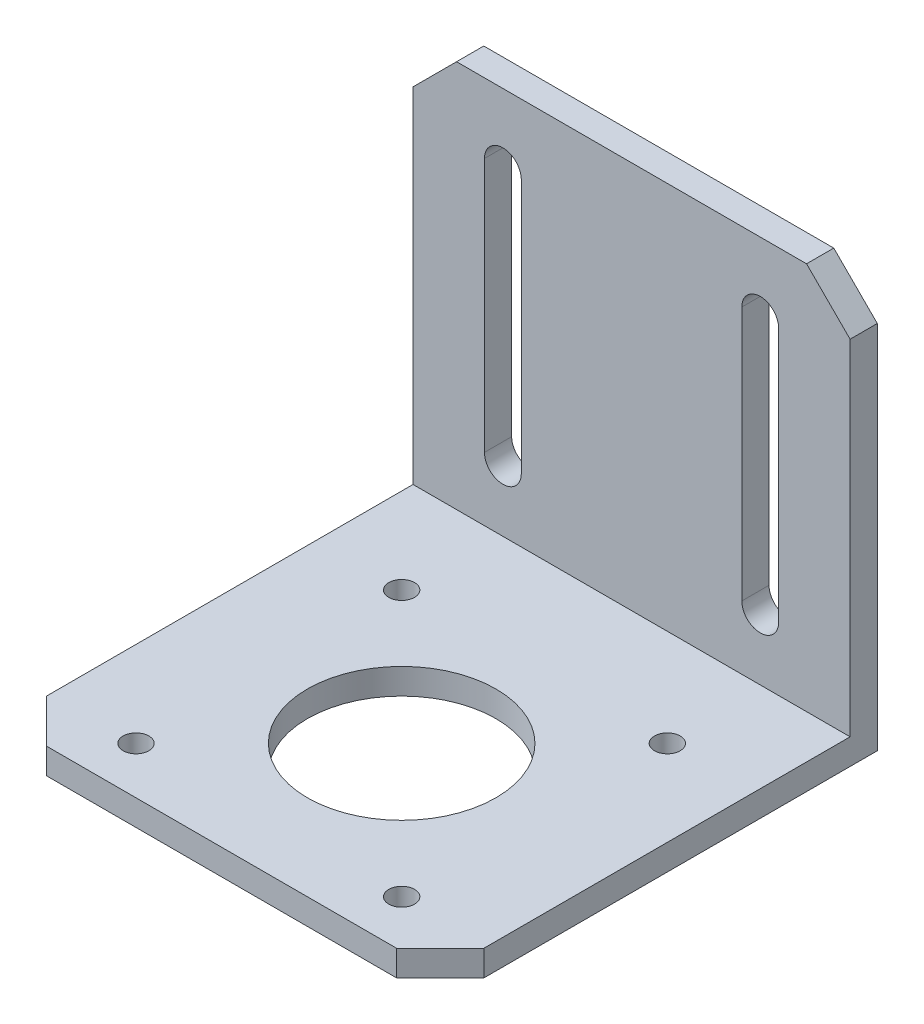
SolidWorks part; units mm, degrees
ref_plane "Front Plane" through (0, 0, 0) normal (0, 0, 1) x (1, 0, 0)
ref_plane "Top Plane" through (0, 0, 0) normal (0, 1, 0) x (1, 0, 0)
ref_plane "Right Plane" through (0, 0, 0) normal (1, 0, 0) x (0, 0, -1)
sketch "Sketch1" plane through (0, 0, 0) normal (0, 1, 0) x (1, 0, 0)
  line L0 (0, -1000) -> (0, 49000) construction
  line L5 (20.42, -21) -> (-20.42, -21)
  line L6 (25.5, -15.92) -> (25.5, 30)
  line L7 (25.5, 30) -> (-25.5, 30)
  line L8 (-25.5, -15.92) -> (-25.5, 30)
  line L9 (-1000, 0) -> (49000, 0) construction
  line L10 (25.5, -15.92) -> (20.42, -21)
  line L11 (-20.42, -21) -> (-25.5, -15.92)
  circle A5 centre (0, 0) radius 11
  circle A6 centre (15.5, -15.5) radius 1.5
  circle A7 centre (-15.5, -15.5) radius 1.5
  circle A8 centre (-15.5, 15.5) radius 1.5
  circle A10 centre (15.5, 15.5) radius 1.5
  point P2 (25.5, -21)
  point P5 (-25.5, -21)
  dimension "D3" = 51
  dimension "D4" = 51
  dimension "D1" = 22
  dimension "D5" = 3
  dimension "D2" = 21
  dimension "D6" = 31
  dimension "D7" = 31
extrude "Boss-Extrude1" add sketch "Sketch1" along normal blind 3
sketch "Sketch2" plane through (0, 0, -30) normal (0, 0, 1) x (1, 0, 0)
  line L0 (0, 41.0349) -> (0, -49958.9651) construction
  line L1 (-25.5, 0) -> (25.5, 0)
  line L2 (-25.5, 0) -> (-25.5, 43.18)
  line L3 (-20.42, 48.26) -> (20.42, 48.26)
  line L4 (25.5, 0) -> (25.5, 43.18)
  line L6 (-17.165, 40.11) -> (-17.165, 10.41)
  line L8 (-12.865, 40.11) -> (-12.865, 10.41)
  line L9 (12.865, 40.11) -> (12.865, 10.41)
  line L10 (17.165, 40.11) -> (17.165, 10.41)
  line L11 (20.42, 48.26) -> (25.5, 43.18)
  line L12 (-25.5, 43.18) -> (-20.42, 48.26)
  arc A0 (-17.165, 40.11) -> (-12.865, 40.11) centre (-15.015, 40.11) cw
  arc A1 (-17.165, 10.41) -> (-12.865, 10.41) centre (-15.015, 10.41) ccw
  arc A2 (17.165, 40.11) -> (12.865, 40.11) centre (15.015, 40.11) ccw
  arc A3 (17.165, 10.41) -> (12.865, 10.41) centre (15.015, 10.41) cw
  point P1 (25.5, 48.26)
  point P2 (-25.5, 48.26)
  point P14 (0, 0)
  point P23 (-15.015, 42.26)
  point P24 (-15.015, 8.26)
  dimension "D1" = 51
  dimension "D2" = 48.26
  dimension "D3" = 34
  dimension "D4" = 4.3
  dimension "D5" = 25.73
  dimension "D6" = 8.15
extrude "Boss-Extrude2" add sketch "Sketch2" along normal blind 3.175
